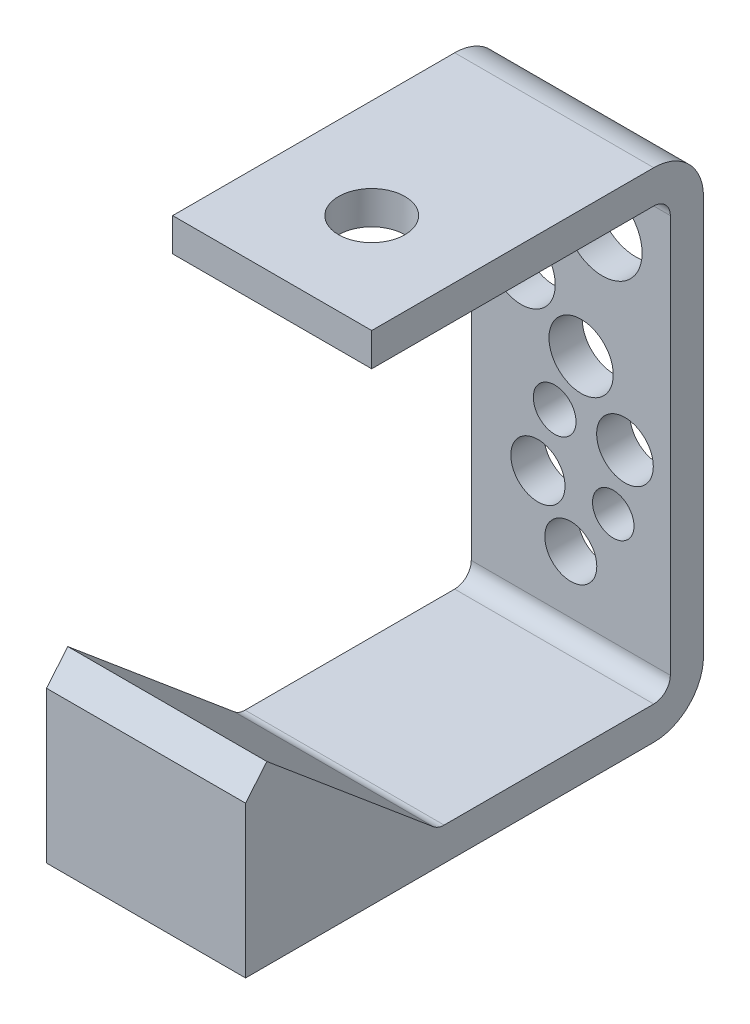
SolidWorks part; units mm, degrees
ref_plane "front" through (0, 0, 0) normal (0, 0, 1) x (1, 0, 0)
ref_plane "top" through (0, 0, 0) normal (0, 1, 0) x (1, 0, 0)
ref_plane "right" through (0, 0, 0) normal (1, 0, 0) x (0, 0, -1)
sketch "Sketch1" plane through (0, 0, 0) normal (1, 0, 0) x (0, 0, -1)
  line L0 (0, 0) -> (0, 82.55)
  line L1 (0, 82.55) -> (-57.15, 82.55)
  line L4 (-77.2165, 27.4943) -> (-44.45, 0)
  line L5 (-44.45, 0) -> (0, 0)
  dimension "D1" = 82.55
  dimension "D2" = 57.15
  dimension "D3" = 40
  dimension "D4" = 42.7736
  dimension "D5" = 44.45
extrude "Base-Extrude-Thin" add sketch "Sketch1" along normal mid plane 38.1 thin
sketch "Sketch2" plane through (0, 88.9, 0) normal (0, 1, 0) x (-1, 0, 0)
  line L0 (0, 50) -> (0, -50) construction
  line L1 (-19.05, 57.15) -> (19.05, 57.15) construction
  circle A0 centre (0, 38.1) radius 6.35
  dimension "D1" = 12.7
  dimension "D2" = 19.05
extrude "Cut-Extrude1" cut sketch "Sketch2" against normal up to next
sketch "Sketch3" plane through (0, 0, 0) normal (1, 0, 0) x (0, 0, -1)
  line L0 (-81.2982, 22.63) -> (-81.2982, -6.35)
  line L1 (-81.2982, -6.35) -> (-28.6776, -6.35)
  line L2 (-43.2944, -6.35) -> (-3.175, -6.35) construction
  line L3 (-81.2982, 22.63) -> (-49.4169, -4.1216) construction
  line L4 (-81.2982, 22.63) -> (-49.4169, -4.1216)
  arc A0 (-49.4169, -4.1216) -> (-43.2944, -6.35) centre (-43.2944, 3.175) ccw construction
  arc A1 (-49.4169, -4.1216) -> (-43.2944, -6.35) centre (-43.2944, 3.175) ccw
extrude "Boss-Extrude1" add sketch "Sketch3" along normal up to surface and the other way through all contours A1 L4 L0 L1
sketch "Sketch4" plane through (0, 0, -6.35) normal (0, 0, -1) x (-1, 0, 0)
  circle A0 centre (-6.0486, 70.4689) radius 7.6024
  circle A1 centre (-1.9751, 47.5088) radius 6.1498
  circle A2 centre (9.505, 56.8903) radius 6.5284
  circle A3 centre (3.086, 36.1522) radius 4.0866
  circle A4 centre (-8.1249, 24.4253) radius 3.966
  circle A5 centre (6.2955, 24.4253) radius 5.186
  circle A6 centre (0, 14.1796) radius 4.9761
  circle A7 centre (-10.3691, 36.1522) radius 5.423
extrude "Cut-Extrude2" cut sketch "Sketch4" against normal up to next
